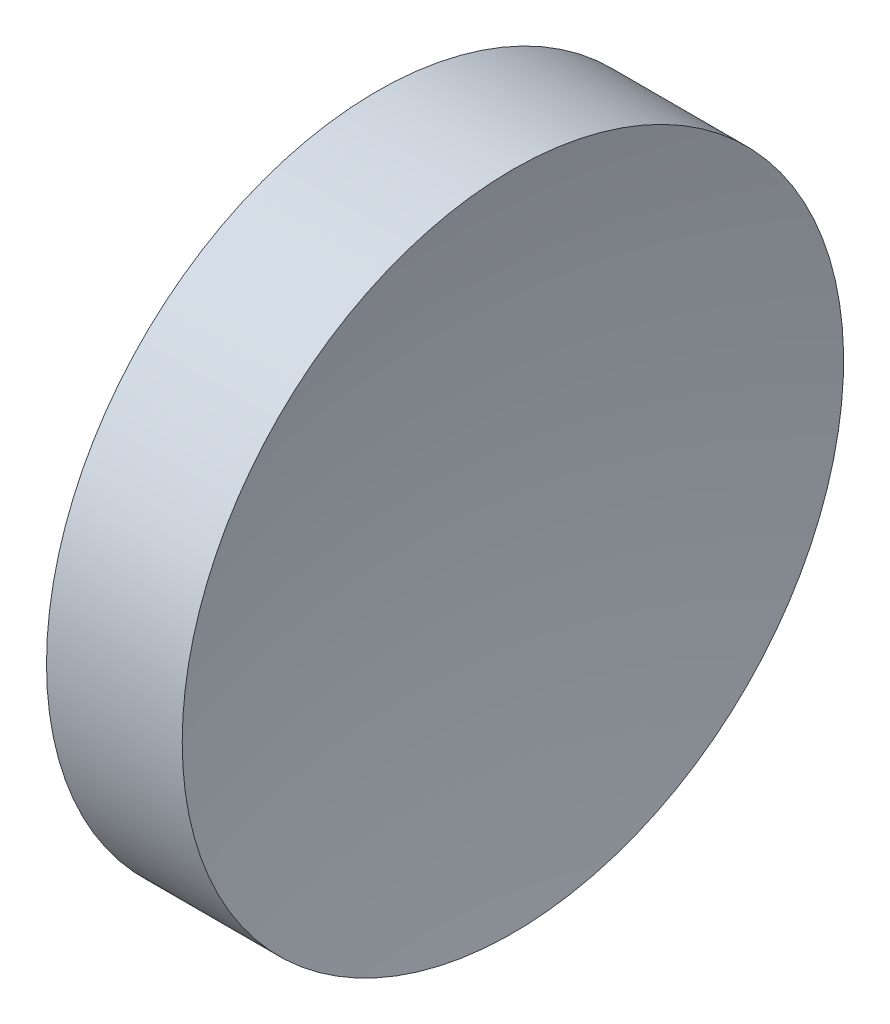
SolidWorks part; units mm, degrees
ref_plane "前视基准面" through (0, 0, 0) normal (0, 0, 1) x (1, 0, 0)
ref_plane "上视基准面" through (0, 0, 0) normal (0, 1, 0) x (1, 0, 0)
ref_plane "右视基准面" through (0, 0, 0) normal (1, 0, 0) x (0, 0, -1)
sketch "草图1" plane through (0, 0, 0) normal (0, 0, 1) x (1, 0, 0)
  line L0 (44.7821, 28.4776) -> (52.988, 28.4776) construction
  line L1 (47.7017, 28.4776) -> (47.7017, 33.4776)
  line L2 (49.2017, 28.4776) -> (47.7017, 28.4776)
  line L3 (47.7017, 33.4776) -> (49.7537, 33.4776)
  arc A0 (49.7537, 33.4776) -> (49.2017, 28.4776) centre (72.1217, 28.4776) ccw
revolve "旋转1" add sketch "草图1" angle 360 about L0
